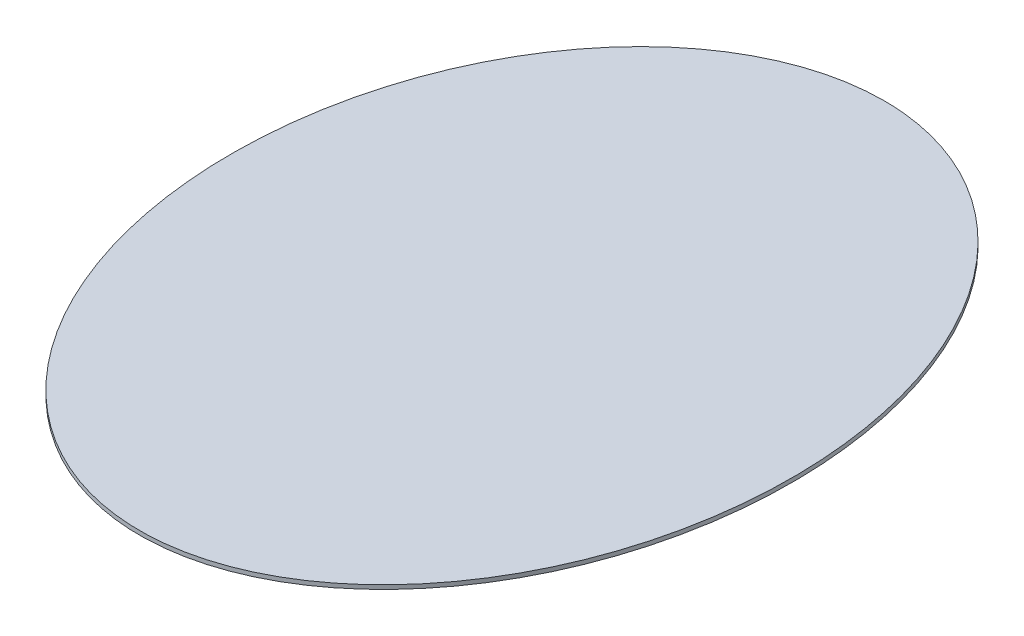
SolidWorks part; units mm, degrees
ref_plane "Front Plane" through (0, 0, 0) normal (0, 0, 1) x (1, 0, 0)
ref_plane "Top Plane" through (0, 0, 0) normal (0, 1, 0) x (1, 0, 0)
ref_plane "Right Plane" through (0, 0, 0) normal (1, 0, 0) x (0, 0, -1)
sketch "Sketch1" plane through (0, 0, 0) normal (0, 1, 0) x (1, 0, 0)
  ellipse E0 centre (0, 0) end of major axis (0, 355) minor radius 265 construction
  ellipse E1 centre (0, 0) end of major axis (0, 365) minor radius 275
  dimension "D1" = 530
  dimension "D2" = 710
  dimension "D3" = 550
  dimension "D4" = 730
extrude "Boss-Extrude1" add sketch "Sketch1" along normal blind 4
sketch "Sketch2" plane through (0, 0, 0) normal (0, -1, 0) x (1, 0, 0)
  line L0 (0, 0) -> (557.7181, 0) construction
